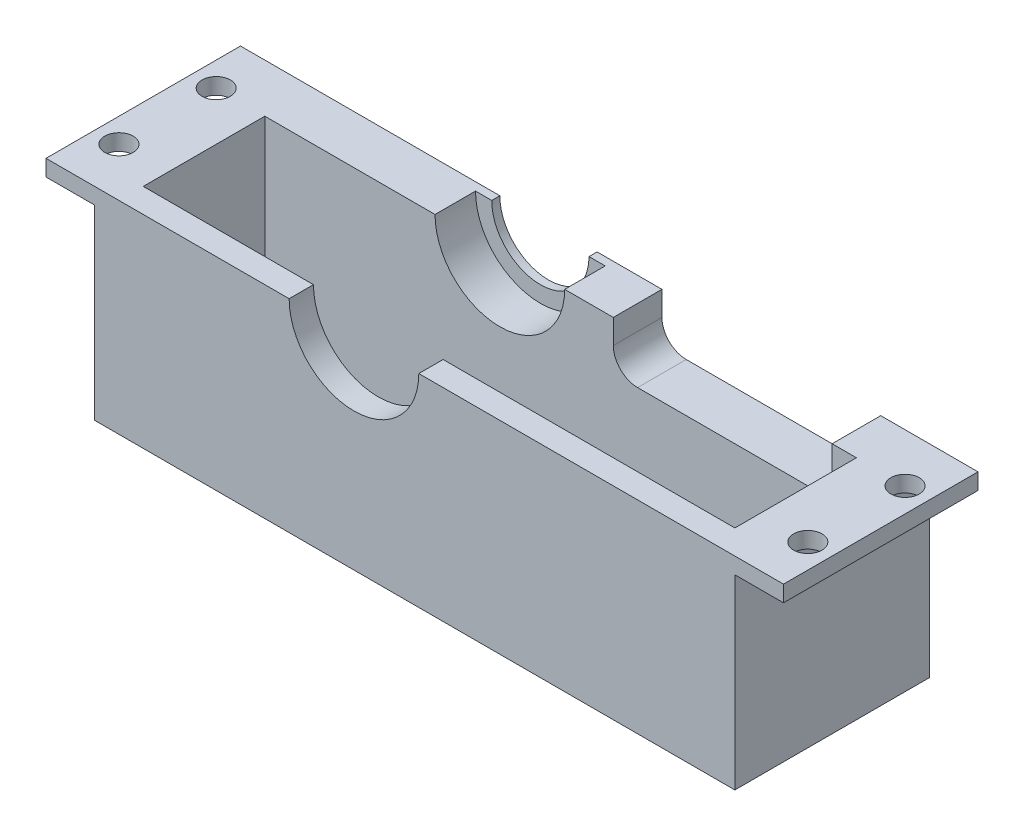
SolidWorks part; units mm, degrees
ref_plane "Alzado" through (0, 0, 0) normal (0, 0, 1) x (1, 0, 0)
ref_plane "Planta" through (0, 0, 0) normal (0, 1, 0) x (1, 0, 0)
ref_plane "Vista lateral" through (0, 0, 0) normal (1, 0, 0) x (0, 0, -1)
sketch "Croquis1" plane through (0, 0, 0) normal (0, 0, 1) x (1, 0, 0)
  line L2 (79, 25) -> (79, 0)
  line L3 (79, 0) -> (0, 0)
  line L4 (0, 0) -> (0, 25)
  line L5 (0, 25) -> (40, 25)
  line L10 (79, 25) -> (40, 25)
  circle A1 centre (32, 25) radius 8
  dimension "D6" = 16
  dimension "D1" = 47
  dimension "D2" = 32
  dimension "D3" = 25
extrude "Saliente-Extruir1" add sketch "Croquis1" along normal blind 3
sketch "Croquis4" plane through (0, 0, 0) normal (0, 0, -1) x (-1, 0, 0)
  line L0 (-79, 0) -> (0, 0) construction
  line L1 (-79, 25) -> (-76, 25)
  line L2 (-79, 25) -> (-79, 0)
  line L3 (-79, 0) -> (-76, 0)
  line L4 (-76, 25) -> (-76, 0)
  line L5 (0, 25) -> (-3, 25)
  line L10 (0, 25) -> (0, 0)
  line L11 (0, 0) -> (-3, 0)
  line L12 (-3, 25) -> (-3, 0)
  dimension "D1" = 3
  dimension "D2" = 3
extrude "Saliente-Extruir4" add sketch "Croquis4" along normal blind 15
sketch "Croquis6" plane through (0, 0, -15) normal (0, 0, -1) x (-1, 0, 0)
  line L7 (-79, 25) -> (-79, 0) construction
  line L8 (-79, 25) -> (-79, 0)
  line L9 (-79, 0) -> (0, 0)
  line L10 (0, 0) -> (0, 25)
  line L11 (0, 25) -> (-24, 25)
  line L13 (0, 0) -> (0, 25) construction
  line L14 (-79, 25) -> (-73, 25)
  line L15 (-73, 25) -> (-73, 19)
  line L16 (-73, 19) -> (-46, 19)
  line L17 (-46, 19) -> (-46, 25)
  line L18 (-46, 25) -> (-40, 25)
  line L19 (-76, 25) -> (-79, 25) construction
  arc A4 (-40, 25) -> (-24, 25) centre (-32, 25) ccw
  dimension "D1" = 6
  dimension "D2" = 6
  dimension "D3" = 6
extrude "Saliente-Extruir6" add sketch "Croquis6" along normal blind 5
sketch "Croquis11" plane through (76, 0, 0) normal (1, 0, 0) x (0, 0, -1)
  line L1 (-3, 0) -> (20, 0)
  line L2 (-3, 0) -> (-3, 2)
  line L3 (-3, 2) -> (20, 2)
  line L4 (20, 0) -> (20, 2)
  dimension "D1" = 2
extrude "Saliente-Extruir11" add sketch "Croquis11" against normal blind 6
sketch "Croquis12" plane through (3, 0, 0) normal (-1, 0, 0) x (0, 0, 1)
  line L1 (-20, 0) -> (3, 0)
  line L2 (-20, 0) -> (-20, 2)
  line L3 (-20, 2) -> (3, 2)
  line L4 (3, 0) -> (3, 2)
  dimension "D1" = 2
extrude "Saliente-Extruir12" add sketch "Croquis12" against normal blind 6
sketch "Croquis24" plane through (0, 0, -20) normal (0, 0, -1) x (-1, 0, 0)
  line L0 (-79, 0) -> (-79, 25)
  line L2 (-73, 25) -> (-73, 19)
  line L3 (-73, 19) -> (-46, 19)
  line L4 (-40, 25) -> (-38, 25)
  line L6 (-46, 19) -> (-46, 25)
  line L7 (-46, 25) -> (-40, 25)
  line L8 (-79, 0) -> (0, 0)
  line L9 (0, 0) -> (0, 25)
  line L10 (0, 25) -> (-26, 25)
  line L14 (-79, 25) -> (-73, 25)
  arc A0 (-38, 25) -> (-26, 25) centre (-32, 25) ccw
  arc A1 (-40, 25) -> (-24, 25) centre (-32, 25) ccw construction
  dimension "D2" = 12
extrude "Saliente-Extruir23" add sketch "Croquis24" along normal blind 1
sketch "Croquis27" plane through (79, 0, 0) normal (1, 0, 0) x (0, 0, -1)
  line L0 (21, 25) -> (21, 0) construction
  line L1 (-3, 25) -> (21, 25)
  line L2 (-3, 25) -> (-3, 23)
  line L3 (-3, 23) -> (21, 23)
  line L4 (21, 25) -> (21, 23)
  dimension "D1" = 2
extrude "Saliente-Extruir26" add sketch "Croquis27" along normal blind 6
sketch "Croquis28" plane through (0, 0, 0) normal (-1, 0, 0) x (0, 0, 1)
  line L1 (-21, 25) -> (3, 25)
  line L2 (-21, 25) -> (-21, 23)
  line L3 (-21, 23) -> (3, 23)
  line L4 (3, 25) -> (3, 23)
  line L5 (3, 0) -> (3, 25) construction
  dimension "D1" = 2
extrude "Saliente-Extruir27" add sketch "Croquis28" along normal blind 6
sketch "Croquis13" plane through (0, 25, 0) normal (0, 1, 0) x (1, 0, 0)
  line L0 (85, -3) -> (40, -3) construction
  line L1 (70, 15) -> (76, 15) construction
  line L2 (76, 0) -> (70, 0) construction
  line L7 (76, 15) -> (76, 0) construction
  line L10 (39.5, -6) -> (39.5, 21) construction
  line L11 (38, 21) -> (46, 21) construction
  line L12 (73, 21) -> (85, 21) construction
  line L15 (85, 21) -> (85, -3) construction
  circle A3 centre (82, 15) radius 1.75
  circle A4 centre (82, 3) radius 1.75
  circle A7 centre (73, 11) radius 1.75
  circle A8 centre (73, 4) radius 1.75
  circle A11 centre (6, 4) radius 1.75
  circle A12 centre (6, 11) radius 1.75
  circle A13 centre (-3, 3) radius 1.75
  circle A14 centre (-3, 15) radius 1.75
  dimension "D3" = 3.5
  dimension "D4" = 3.5
  dimension "D5" = 6
  dimension "D6" = 6
  dimension "D7" = 3
  dimension "D8" = 4
  dimension "D9" = 3
  dimension "D10" = 3
  dimension "D11" = 4
  dimension "D13" = 3.5
  dimension "D14" = 3.5
  dimension "D23" = 3
extrude "Cortar-Extruir1" cut sketch "Croquis13" against normal through all both
fillet "Redondeo1" radius 3 2 edges at (73, 19, -18) (46, 19, -18)
